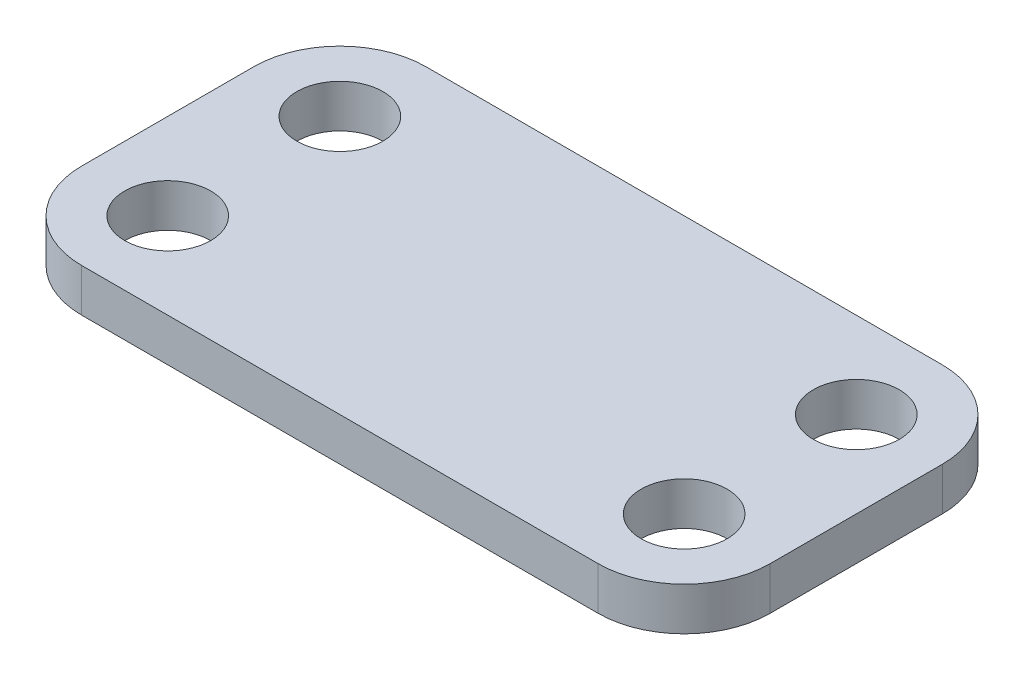
SolidWorks part; units mm, degrees
ref_plane "Front Plane" through (0, 0, 0) normal (0, 0, 1) x (1, 0, 0)
ref_plane "Top Plane" through (0, 0, 0) normal (0, 1, 0) x (1, 0, 0)
ref_plane "Right Plane" through (0, 0, 0) normal (1, 0, 0) x (0, 0, -1)
sketch "Sketch2" plane through (0, 0, 0) normal (0, 1, 0) x (1, 0, 0)
  line L1 (-19.05, -12.7) -> (19.05, -12.7)
  line L2 (-25.4, -6.35) -> (-25.4, 6.35)
  line L3 (-19.05, 12.7) -> (19.05, 12.7)
  line L4 (25.4, -6.35) -> (25.4, 6.35)
  line L5 (0, 12.7) -> (0, -12.7) construction
  line L6 (-25.4, 0) -> (25.4, 0) construction
  arc A0 (-19.05, -12.7) -> (-25.4, -6.35) centre (-19.05, -6.35) cw
  arc A1 (19.05, -12.7) -> (25.4, -6.35) centre (19.05, -6.35) ccw
  arc A2 (25.4, 6.35) -> (19.05, 12.7) centre (19.05, 6.35) ccw
  arc A3 (-25.4, 6.35) -> (-19.05, 12.7) centre (-19.05, 6.35) cw
  circle A4 centre (-19.05, 6.35) radius 3.175
  circle A5 centre (-19.05, -6.35) radius 3.175
  circle A6 centre (19.05, 6.35) radius 3.175
  circle A7 centre (19.05, -6.35) radius 3.175
  point P0 (0, 0)
  dimension "D1" = 6.35
  dimension "D4" = 6.35
  dimension "D2" = 50.8
  dimension "D3" = 25.4
extrude "Boss-Extrude1" add sketch "Sketch2" along normal blind 3.175
